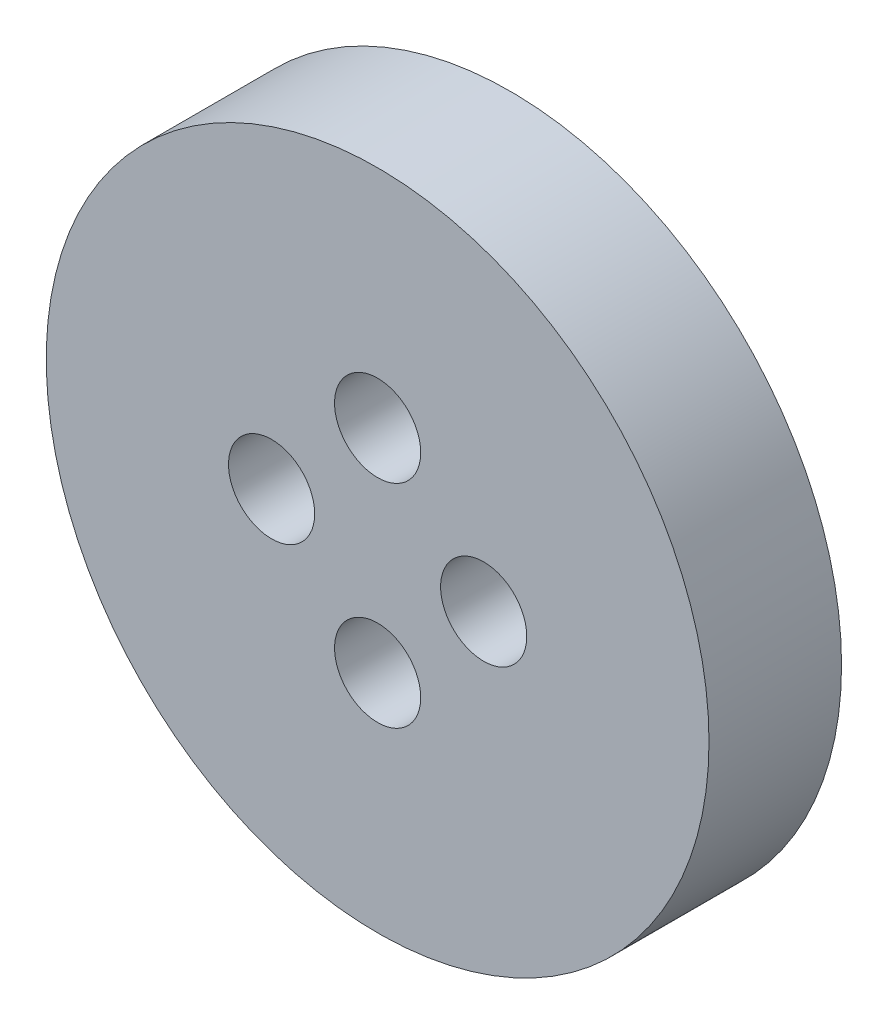
SolidWorks part; units mm, degrees
ref_plane "正面" through (0, 0, 0) normal (0, 0, 1) x (1, 0, 0)
ref_plane "平面" through (0, 0, 0) normal (0, 1, 0) x (1, 0, 0)
ref_plane "右側面" through (0, 0, 0) normal (1, 0, 0) x (0, 0, -1)
sketch "ｽｹｯﾁ1" plane through (0, 0, 0) normal (0, 0, 1) x (1, 0, 0)
  line L0 (-54.6319, 0) -> (58.4452, 0) construction
  line L1 (0, 46.6388) -> (0, -43.2656) construction
  circle A0 centre (0, 0) radius 25
  circle A1 centre (8, 0) radius 1.75
  circle A2 centre (0, -8) radius 1.75
  circle A3 centre (-8, 0) radius 1.75
  circle A4 centre (0, 8) radius 1.75
  point P9 (0, 0)
  point P10 (0, 0)
  point P11 (-7.8701, 9.0157)
  point P18 (0, 0)
  point P19 (0, 0)
  dimension "D1" = 50
  dimension "D2" = 3.5
  dimension "D3" = 8
  dimension "D4" = 4
extrude "ﾎﾞｽ - 押し出し1" add sketch "ｽｹｯﾁ1" along normal blind 10
sketch "ｽｹｯﾁ2" plane through (0, 0, 10) normal (0, 0, 1) x (1, 0, 0)
  circle A1 centre (0, 8) radius 3.25
  circle A2 centre (8, 0) radius 3.25
  circle A3 centre (0, -8) radius 3.25
  circle A4 centre (-8, 0) radius 3.25
  point P1 (-17.1302, -2.4553)
  point P2 (0, 0)
  point P5 (-14.6217, -0.8281)
  point P12 (0, 0)
  dimension "D1" = 6.5
  dimension "D2" = 4
extrude "ｶｯﾄ - 押し出し1" cut sketch "ｽｹｯﾁ2" against normal blind 5 contours A1 | A4 | A3 | A2
